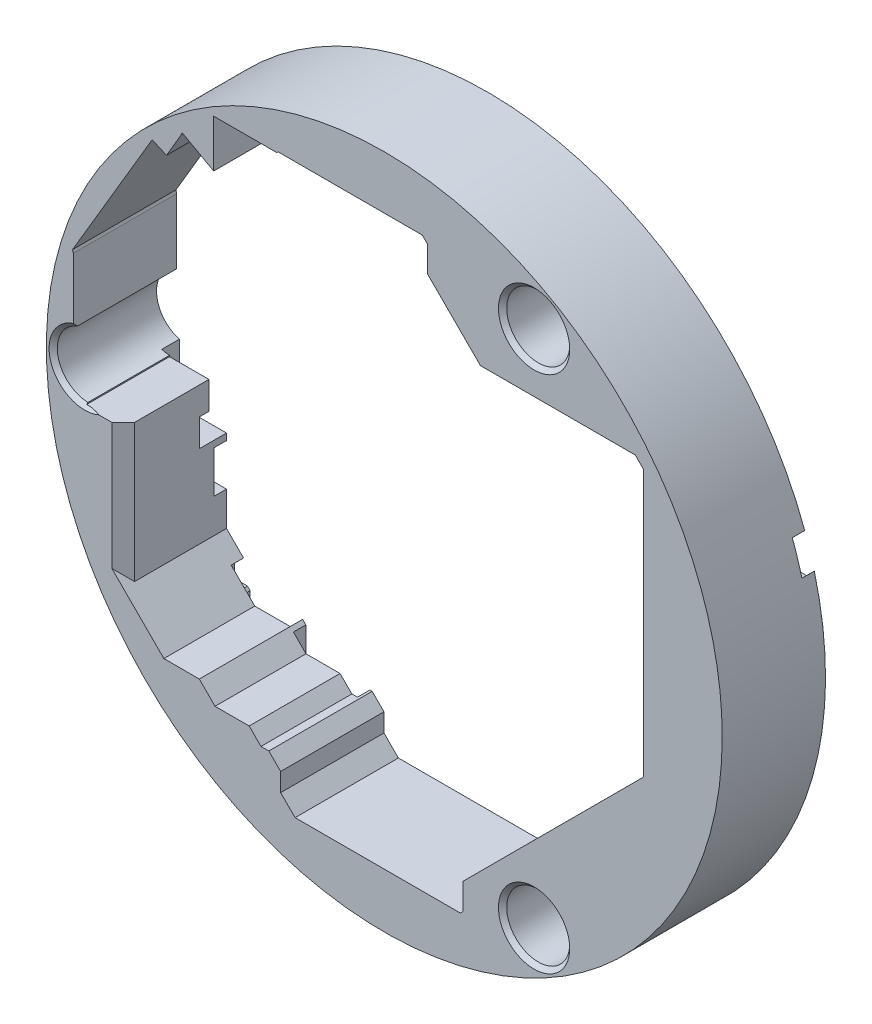
SolidWorks part; units mm, degrees
material "丙烯酸(中高冲击)"
ref_plane "前视基准面" through (0, 0, 0) normal (0, 0, 1) x (1, 0, 0)
ref_plane "上视基准面" through (0, 0, 0) normal (0, 1, 0) x (1, 0, 0)
ref_plane "右视基准面" through (0, 0, 0) normal (1, 0, 0) x (0, 0, -1)
sketch "草图1" plane through (0, 0, 0) normal (0, 0, 1) x (1, 0, 0)
  line L0 (72.39, 79.248) -> (74.422, 77.216)
  line L1 (71.882, 79.248) -> (72.39, 79.248)
  line L2 (71.501, 79.629) -> (71.882, 79.248)
  line L3 (70.866, 79.629) -> (71.501, 79.629)
  line L4 (69.596, 80.899) -> (69.596, 85.598)
  line L5 (69.596, 80.899) -> (70.866, 79.629)
  line L6 (74.422, 59.944) -> (74.422, 77.216)
  line L7 (74.422, 59.944) -> (78.359, 56.007)
  line L8 (78.359, 56.007) -> (81.788, 56.007)
  line L9 (81.788, 56.007) -> (83.312, 54.483)
  line L10 (83.312, 54.483) -> (86.614, 54.483)
  line L11 (86.614, 54.483) -> (87.757, 53.34)
  line L12 (87.757, 53.34) -> (88.519, 53.34)
  line L13 (88.519, 53.34) -> (89.662, 52.197)
  line L14 (89.662, 50.419) -> (89.662, 52.197)
  line L15 (89.662, 50.419) -> (91.059, 49.022)
  line L16 (91.059, 49.022) -> (107.061, 49.022)
  line L17 (107.061, 49.022) -> (107.315, 49.276)
  line L18 (107.315, 49.276) -> (107.315, 51.816)
  line L19 (107.315, 51.816) -> (122.809, 67.31)
  line L20 (122.809, 67.31) -> (122.809, 94.234)
  line L21 (121.158, 95.885) -> (122.809, 94.234)
  line L22 (106.172, 95.885) -> (121.158, 95.885)
  line L23 (103.886, 98.171) -> (106.172, 95.885)
  line L24 (103.886, 98.171) -> (103.886, 103.505)
  line L25 (103.378, 104.013) -> (103.886, 103.505)
  line L26 (89.408, 104.013) -> (103.378, 104.013)
  line L27 (89.281, 103.886) -> (89.408, 104.013)
  line L28 (89.281, 99.568) -> (89.281, 103.886)
  line L29 (88.265, 98.552) -> (89.281, 99.568)
  line L30 (84.6179, 98.4897) -> (88.265, 98.552)
  line L31 (82.677, 99.568) -> (84.6179, 98.4897)
  line L32 (80.137, 100.965) -> (82.677, 99.568)
  line L33 (80.01, 100.711) -> (80.137, 100.965)
  line L34 (77.2235, 98.9286) -> (78.6174, 98.3238)
  line L35 (69.5238, 85.8781) -> (77.2235, 98.9286)
  line L36 (69.5238, 85.8781) -> (69.596, 85.598)
  line L37 (78.6174, 98.3238) -> (80.01, 100.711)
sketch "草图2" plane through (0, 0, 0) normal (0, 0, 1) x (1, 0, 0)
  circle A0 centre (114.195, 101.5687) radius 3.05
  circle A3 centre (114.1951, 51.3391) radius 3.05
  circle A6 centre (70.6948, 76.454) radius 3.05
  circle A9 centre (99.695, 76.454) radius 32.7112
extrude "凸台-拉伸1" add sketch "草图2" along normal blind 10
extrude "切除-拉伸1" cut sketch "草图1" along normal up to surface (10 mm away) up to face at (117.2451, 51.3391, 10)
sketch "草图3" plane through (0, 0, 0) normal (0, 0, 1) x (1, 0, 0)
  line L1 (69.596, 80.899) -> (74.422, 80.899)
  line L2 (69.596, 80.899) -> (69.596, 77.216)
  line L3 (69.596, 77.216) -> (74.422, 77.216)
  line L4 (74.422, 80.899) -> (74.422, 77.216)
extrude "切除-拉伸2" cut sketch "草图3" along normal up to surface (10 mm away) up to face at (117.2451, 51.3391, 10)
sketch "草图4" plane through (0, 0, 0) normal (0, 0, 1) x (1, 0, 0)
  circle A0 centre (128.695, 76.454) radius 3.1
  circle A3 centre (85.195, 51.339) radius 3.1
  circle A6 centre (85.195, 101.569) radius 3.1
extrude "切除-拉伸3" cut sketch "草图4" along normal blind 1.2
sketch "草图5" plane through (0, 0, 0) normal (0, 0, 1) x (1, 0, 0)
  line L5 (88.265, 98.0709) -> (82.133, 98.0709)
  line L6 (88.265, 98.0709) -> (88.265, 101.9047)
  line L7 (88.265, 101.9047) -> (82.133, 101.9047)
  line L8 (82.133, 98.0709) -> (82.133, 101.9047)
  line L9 (88.2954, 51.3382) -> (82.095, 51.3382)
  line L10 (88.2954, 51.3382) -> (88.2954, 56.6846)
  line L11 (88.2954, 56.6846) -> (82.095, 56.6846)
  line L12 (82.095, 51.3382) -> (82.095, 56.6846)
extrude "切除-拉伸7" cut sketch "草图5" along normal blind 1.2
sketch "草图6" plane through (0, 0, 0) normal (0, 0, 1) x (1, 0, 0)
  line L0 (70.739, 63.246) -> (70.739, 67.31)
  line L1 (70.739, 63.246) -> (74.803, 63.246)
  line L2 (74.803, 63.246) -> (74.803, 67.31)
  line L3 (70.739, 67.31) -> (74.803, 67.31)
  line L4 (75.692, 58.293) -> (81.788, 58.293)
  line L5 (81.788, 53.34) -> (81.788, 58.293)
  line L6 (78.105, 53.34) -> (81.788, 53.34)
  line L7 (77.851, 53.594) -> (78.105, 53.34)
  line L8 (77.851, 53.594) -> (77.851, 54.102)
  line L9 (77.724, 54.229) -> (77.851, 54.102)
  line L10 (76.962, 54.229) -> (77.724, 54.229)
  line L11 (76.708, 54.483) -> (76.962, 54.229)
  line L12 (76.708, 54.483) -> (76.708, 55.88)
  line L13 (76.454, 56.134) -> (76.708, 55.88)
  line L14 (75.438, 56.134) -> (76.454, 56.134)
  line L15 (75.184, 56.388) -> (75.438, 56.134)
  line L16 (75.184, 56.388) -> (75.184, 58.293)
  line L17 (75.184, 58.293) -> (76.327, 58.293)
  line L18 (94.742, 100.457) -> (103.886, 100.457)
  line L19 (94.742, 100.457) -> (94.742, 104.394)
  line L20 (103.886, 100.457) -> (103.886, 107.188)
  line L21 (94.742, 107.188) -> (103.886, 107.188)
  line L22 (94.742, 104.394) -> (94.742, 107.188)
  line L23 (131.318, 84.074) -> (131.318, 87.757)
  line L24 (123.952, 87.757) -> (131.318, 87.757)
  line L25 (123.952, 84.074) -> (131.318, 84.074)
  line L26 (123.952, 84.074) -> (123.952, 87.757)
extrude "切除-拉伸8" cut sketch "草图6" along normal blind 1.2 contours L17 L16 L15 L14 L13 L12 L11 L10 L9 L8 L7 L6 L5 L4 | L3 L0 L1 L2 | L26 L25 L23 L24 | L22 L19 L18 L20 L21
sketch "草图7" plane through (0, 0, 0) normal (0, 0, 1) x (1, 0, 0)
  line L0 (94.107, 102.997) -> (94.107, 106.553)
  line L1 (89.281, 102.997) -> (94.107, 102.997)
  line L2 (89.281, 102.997) -> (89.281, 106.553)
  line L3 (89.281, 106.553) -> (94.107, 106.553)
  line L4 (74.549, 67.945) -> (75.057, 67.945)
  line L5 (75.057, 67.945) -> (75.057, 70.612)
  line L6 (69.723, 70.612) -> (75.057, 70.612)
  line L7 (69.723, 67.945) -> (69.723, 70.612)
  line L8 (69.723, 67.945) -> (74.549, 67.945)
extrude "切除-拉伸9" cut sketch "草图7" along normal blind 2.6
chamfer "倒角1" distance 0.4 angle 45 3 edges at (69.3002, 73.7415, 10) (117.2451, 51.3391, 10) (117.245, 101.5687, 10)
sketch "草图8" plane through (0, 0, 0) normal (0, 0, 1) x (1, 0, 0)
  line L0 (69.85, 68.072) -> (69.85, 72.39)
  line L1 (69.85, 68.072) -> (74.422, 68.072)
  line L2 (74.422, 68.072) -> (74.422, 71.882)
  line L3 (74.422, 71.882) -> (75.438, 72.898)
  line L4 (75.438, 72.898) -> (75.438, 78.74)
  line L5 (74.93, 79.248) -> (75.438, 78.74)
  line L6 (72.898, 79.248) -> (74.93, 79.248)
  line L7 (72.644, 78.994) -> (72.898, 79.248)
  line L8 (72.644, 73.787) -> (72.644, 78.994)
  line L9 (72.5308, 73.6738) -> (72.644, 73.787)
  line L10 (69.9869, 73.6738) -> (72.5308, 73.6738)
  line L11 (69.85, 73.5369) -> (69.9869, 73.6738)
  line L12 (69.85, 72.39) -> (69.85, 73.5369)
extrude "切除-拉伸10" cut sketch "草图8" along normal blind 1.7
sketch "草图9" plane through (0, 0, 0) normal (0, 0, 1) x (1, 0, 0)
  line L5 (70.6061, 73.2884) -> (75.9503, 73.2884)
  line L6 (70.6061, 73.2884) -> (70.6061, 77.8192)
  line L7 (70.6061, 77.8192) -> (75.9503, 77.8192)
  line L8 (75.9503, 73.2884) -> (75.9503, 77.8192)
extrude "切除-拉伸11" cut sketch "草图9" along normal up to surface (10 mm away) up to face at (117.6451, 51.3391, 10)
chamfer "倒角3" distance 2 angle 45 2 edges at (121.9835, 95.0595, 10) (122.809, 80.772, 10)
sketch "草图10" plane through (0, 0, 0) normal (0, 0, 1) x (1, 0, 0)
  line L1 (89.281, 103.886) -> (83.1811, 103.886)
  line L2 (89.281, 103.886) -> (89.281, 97.8668)
  line L3 (89.281, 97.8668) -> (83.1811, 97.8668)
  line L4 (83.1811, 103.886) -> (83.1811, 97.8668)
extrude "切除-拉伸12" cut sketch "草图10" along normal up to surface (10 mm away) up to face at (117.6451, 51.3391, 10)
chamfer "倒角5" distance 1.1 angle 45 1 edges at (74.422, 66.6162, 10)
chamfer "倒角6" distance 2 angle 45 1 edges at (105.029, 97.028, 10)
